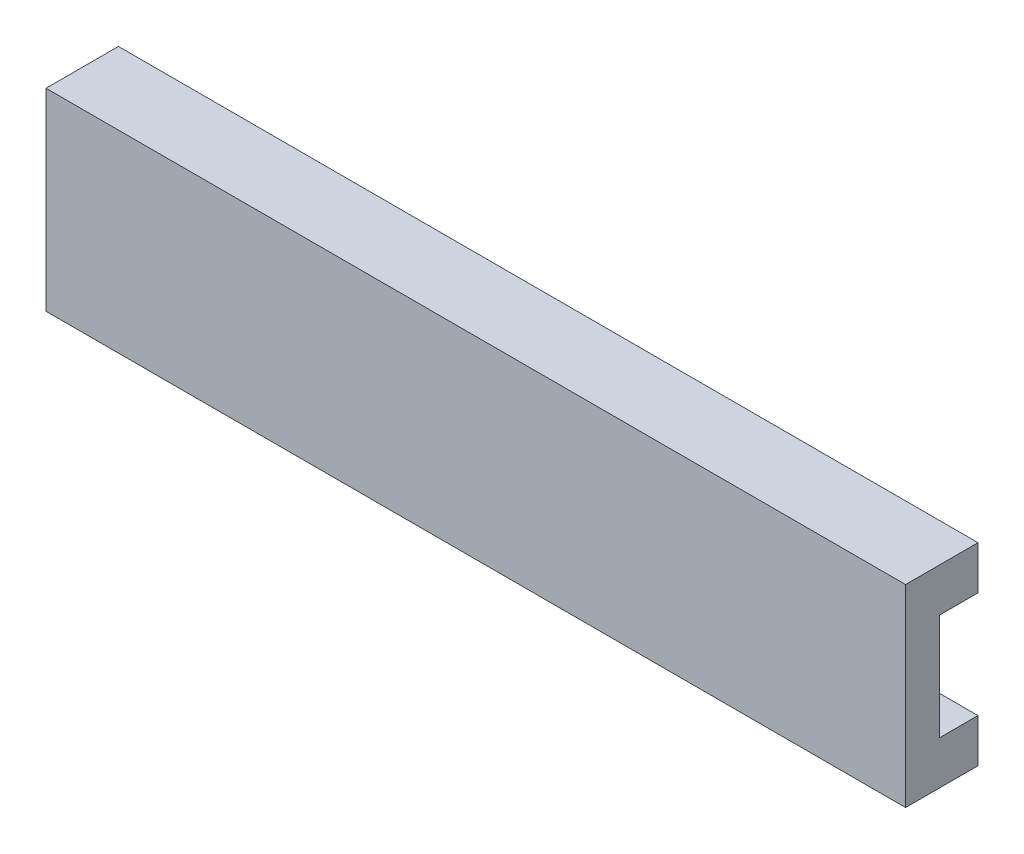
SolidWorks part; units mm, degrees
ref_plane "Front Plane" through (0, 0, 0) normal (0, 0, 1) x (1, 0, 0)
ref_plane "Top Plane" through (0, 0, 0) normal (0, 1, 0) x (1, 0, 0)
ref_plane "Right Plane" through (0, 0, 0) normal (1, 0, 0) x (0, 0, -1)
sketch "Sketch1" plane through (0, 0, 0) normal (1, 0, 0) x (0, 0, -1)
  line L0 (0, 0) -> (0, 40)
  line L1 (0, 40) -> (15, 40)
  line L2 (15, 40) -> (15, 31)
  line L3 (15, 31) -> (7, 31)
  line L4 (7, 31) -> (7, 9)
  line L5 (7, 9) -> (15, 9)
  line L6 (15, 9) -> (15, 0)
  line L7 (15, 0) -> (0, 0)
  dimension "D1" = 9
  dimension "D2" = 9
  dimension "D3" = 8
  dimension "D4" = 15
  dimension "D5" = 15
  dimension "D6" = 40
extrude "Boss-Extrude1" add sketch "Sketch1" against normal blind 178
